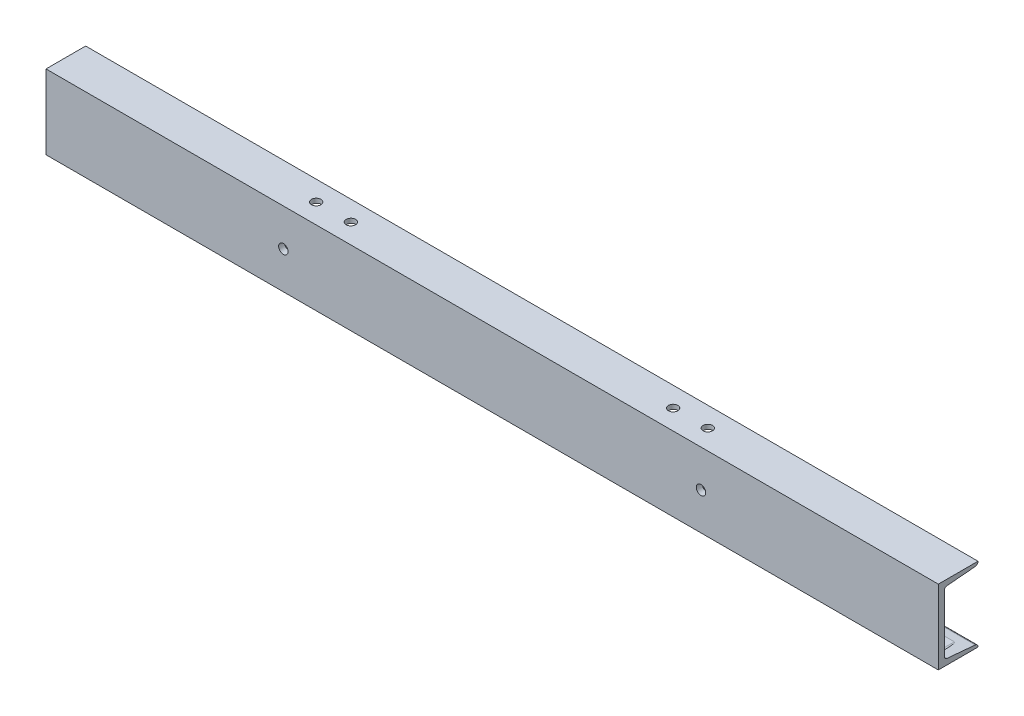
SolidWorks part; units mm, degrees
material "Plain Carbon Steel"
ref_plane "Front Plane" through (0, 0, 0) normal (0, 0, 1) x (1, 0, 0)
ref_plane "Top Plane" through (0, 0, 0) normal (0, 1, 0) x (1, 0, 0)
ref_plane "Right Plane" through (0, 0, 0) normal (1, 0, 0) x (0, 0, -1)
sketch "Sketch1" plane through (0, 0, 0) normal (0, 1, 0) x (1, 0, 0)
  line L0 (-450, 0) -> (450, 0)
  dimension "D1" = 900
other "Structural Member1"
ref_plane "Plane1" through (-450, 0, 0) normal (1, 0, 0) x (0, 0, 1)
sketch "Sketch112" plane through (-450, 0, 0) normal (1, 0, 0) x (0, 0, 1)
  line L0 (0, 37.5) -> (0, -37.5)
  line L1 (0, 37.5) -> (-40, 37.5)
  line L2 (0, -37.5) -> (-40, -37.5)
  line L3 (-6, 28.7531) -> (-6, -28.7531)
  line L4 (-8.7363, 31.7414) -> (-37.2637, 34.2586)
  line L5 (0, 0) -> (-48.9646, 0) construction
  line L6 (-40, 37.2469) -> (-40, 37.5)
  line L7 (-8.7363, -31.7414) -> (-37.2637, -34.2586)
  line L8 (-40, -37.2469) -> (-40, -37.5)
  arc A0 (-6, 28.7531) -> (-8.7363, 31.7414) centre (-9, 28.7531) ccw
  arc A1 (-37.2637, 34.2586) -> (-40, 37.2469) centre (-37, 37.2469) cw
  arc A2 (-6, -28.7531) -> (-8.7363, -31.7414) centre (-9, -28.7531) cw
  arc A3 (-37.2637, -34.2586) -> (-40, -37.2469) centre (-37, -37.2469) ccw
  point P6 (0, 0)
  point P12 (-6, 31.5)
  point P15 (-40, 34.5)
  dimension "D6" = 3
  dimension "D1" = 75
  dimension "D2" = 40
  dimension "D3" = 6
  dimension "D4" = 3
  dimension "D5" = 6
sketch "Sketch12" plane through (0, 0, 0) normal (0, 1, 0) x (1, 0, 0)
  line L0 (-412.5239, 20) -> (413.742, 20) construction
  line L1 (-450, 0) -> (450, 0) construction
  line L2 (0, 0) -> (0, 45.9021) construction
  line L4 (-450, 40) -> (-450, 0) construction
  circle A0 centre (-425, 20) radius 4.7625
  circle A1 centre (425, 20) radius 4.7625
  dimension "D2" = 9.525
  dimension "D1" = 20
  dimension "D3" = 25
extrude "Cut-Extrude1" cut sketch "Sketch12" against normal through all
sketch "Sketch15" plane through (0, 0, -6) normal (0, 0, -1) x (-1, 0, 0)
  line L0 (-425, 105.8991) -> (-425, -40.4286) construction
  line L1 (-375.1366, -28.5) -> (-474.8634, -28.5) construction
  line L3 (-412.5, -28.5) -> (-437.5, -28.5) construction
  line L4 (-412.5, -33.5) -> (-437.5, -33.5)
  line L5 (-412.5, -23.5) -> (-437.5, -23.5)
  line L6 (0, 0) -> (0, -58.1771) construction
  line L7 (412.5, -28.5) -> (437.5, -28.5) construction
  line L8 (412.5, -33.5) -> (437.5, -33.5)
  line L9 (412.5, -23.5) -> (437.5, -23.5)
  line L11 (-450, -37.5) -> (450, -37.5) construction
  arc A0 (-412.5, -33.5) -> (-412.5, -23.5) centre (-412.5, -28.5) ccw
  arc A1 (-437.5, -23.5) -> (-437.5, -33.5) centre (-437.5, -28.5) ccw
  arc A2 (412.5, -33.5) -> (412.5, -23.5) centre (412.5, -28.5) cw
  arc A3 (437.5, -23.5) -> (437.5, -33.5) centre (437.5, -28.5) cw
  ellipse E0 centre (-425, 32.7353) end of major axis (-429.7625, 32.7353) minor radius 0.4202 construction
  point P0 (-425, 32.7353)
  point P11 (-425, -28.5)
  point P16 (-425, -28.5)
  point P26 (425, -28.5)
  dimension "D2" = 5
  dimension "D1" = 9
  dimension "D3" = 25
extrude "Cut-Extrude2" cut sketch "Sketch15" along normal blind 40
sketch "Sketch16" plane through (0, 0, 0) normal (0, 1, 0) x (1, 0, 0)
  line L0 (0, -46.4014) -> (0, 86.4014) construction
  line L1 (-394.0256, 20) -> (394.0256, 20) construction
  circle A0 centre (-197.5, 20) radius 4.7625
  circle A1 centre (-162.5, 20) radius 4.7625
  circle A2 centre (162.5, 20) radius 4.7625
  circle A3 centre (197.5, 20) radius 4.7625
  point P5 (0, 20)
  point P6 (0, 20)
  dimension "D2" = 9.525
  dimension "D1" = 20
  dimension "D3" = 197.5
  dimension "D4" = 35
extrude "Cut-Extrude3" cut sketch "Sketch16" along normal through all
sketch "Sketch17" plane through (0, 0, 0) normal (0, 0, 1) x (1, 0, 0)
  line L0 (0, 0) -> (0, 100.2866) construction
  line L1 (0, 0) -> (-482.0954, 0) construction
  circle A0 centre (-210.6, 0) radius 4.7625
  circle A1 centre (210.6, 0) radius 4.7625
  dimension "D1" = 9.525
  dimension "D2" = 210.6
extrude "Cut-Extrude4" cut sketch "Sketch17" against normal through all
